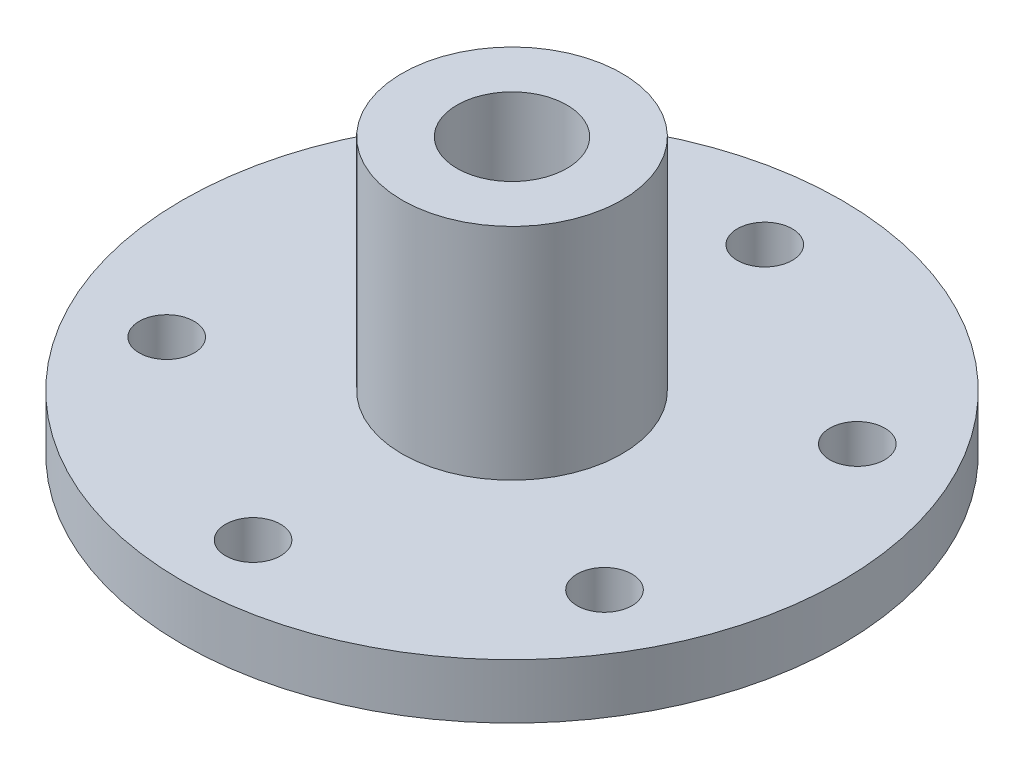
SolidWorks part; units mm, degrees
ref_plane "Front Plane" through (0, 0, 0) normal (0, 0, 1) x (1, 0, 0)
ref_plane "Top Plane" through (0, 0, 0) normal (0, 1, 0) x (1, 0, 0)
ref_plane "Right Plane" through (0, 0, 0) normal (1, 0, 0) x (0, 0, -1)
sketch "Sketch1" plane through (0, 0, 0) normal (0, 1, 0) x (1, 0, 0)
  line L0 (0, 0) -> (0, 23) construction
  line L1 (0, 0) -> (19.9186, 11.5) construction
  line L2 (0, 0) -> (19.9186, -11.5) construction
  line L3 (0, 0) -> (0, -23.561) construction
  line L4 (0, 0) -> (-19.9186, -11.5) construction
  line L5 (0, 0) -> (-19.9186, 11.5) construction
  circle A0 centre (0, 0) radius 30
  circle A2 centre (0, 23) radius 2.5
  circle A3 centre (19.9186, 11.5) radius 2.5
  circle A4 centre (19.9186, -11.5) radius 2.5
  circle A5 centre (0, -23.561) radius 2.5
  circle A6 centre (-19.9186, -11.5) radius 2.5
  circle A7 centre (-19.9186, 11.5) radius 2.5
  dimension "D1" = 60
  dimension "D2" = 60
  dimension "D3" = 60
  dimension "D4" = 60
  dimension "D5" = 60
  dimension "D6" = 60
  dimension "D7" = 60
  dimension "D8" = 23
  dimension "D9" = 23
  dimension "D10" = 23
  dimension "D11" = 23
  dimension "D12" = 23
extrude "Boss-Extrude2" add sketch "Sketch1" along normal blind 5
sketch "Sketch2" plane through (0, 5, 0) normal (0, 1, 0) x (1, 0, 0)
  circle A0 centre (0, 0) radius 10
extrude "Boss-Extrude3" add sketch "Sketch2" along normal blind 20
sketch "Sketch3" plane through (0, 25, 0) normal (0, 1, 0) x (1, 0, 0)
  circle A0 centre (0, 0) radius 5
extrude "Cut-Extrude1" cut sketch "Sketch3" against normal blind 45
